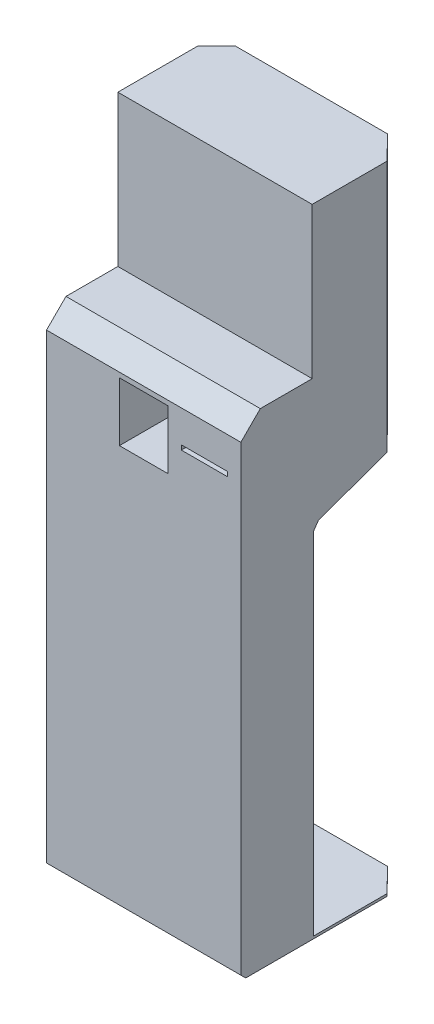
SolidWorks part; units mm, degrees
ref_plane "Front Plane" through (0, 0, 0) normal (0, 0, 1) x (1, 0, 0)
ref_plane "Top Plane" through (0, 0, 0) normal (0, 1, 0) x (1, 0, 0)
ref_plane "Right Plane" through (0, 0, 0) normal (1, 0, 0) x (0, 0, -1)
sketch "Sketch1" plane through (0, 0, 0) normal (1, 0, 0) x (0, 0, -1)
  line L0 (0, 0) -> (-340, 0)
  line L1 (-350, 10) -> (-350, 960)
  line L2 (-310, 1000) -> (-203.2511, 1000)
  line L3 (-203.2511, 1000) -> (-203.2511, 1310.6969)
  line L4 (0, 970) -> (0, 820)
  line L5 (-203.2511, 1310.6969) -> (-350, 1000) construction
  line L6 (-203.2511, 1310.6969) -> (-108.4889, 1310.6969)
  line L7 (-108.4889, 1310.6969) -> (-9.8898, 1028.323) construction
  line L8 (-310, 1000) -> (-350, 960)
  line L9 (-27.4748, 800) -> (-180, 800) construction
  line L10 (-200, 780) -> (-200, 20) construction
  line L11 (-190, 10) -> (0, 10) construction
  line L12 (0, 10) -> (0, 0) construction
  line L13 (-200, 20) -> (-190, 10) construction
  line L14 (-340, 0) -> (-350, 10)
  line L15 (-180, 800) -> (-200, 780) construction
  line L16 (-9.3969, 806.5798) -> (-27.4748, 800)
  line L17 (-27.4748, 800) -> (-190.6031, 740.6262)
  line L18 (-200, 727.206) -> (-200, 5)
  line L19 (0, 1000) -> (0, 1310.6969)
  line L20 (0, 1310.6969) -> (-108.4889, 1310.6969)
  line L21 (-9.8898, 1028.323) -> (0, 970) construction
  line L22 (0, 820) -> (-9.3969, 806.5798)
  line L23 (-190.6031, 740.6262) -> (-200, 727.206)
  line L24 (0, 1000) -> (0, 970)
  line L25 (0, 10) -> (-200, 70) construction
  line L26 (-200, 5) -> (0, 5)
  line L27 (0, 5) -> (0, 0)
  arc A0 (0, 1000) -> (-203.2511, 1310.6969) centre (-339.0968, 1000) ccw construction
  arc A1 (-350, 960) -> (-310, 1000) centre (-310, 960) cw construction
  point P1 (-350, 0)
  point P12 (0, 800)
  point P13 (-200, 800)
  point P15 (-200, 10)
  point P23 (0, 810)
  point P25 (-200, 737.206)
  dimension "D5" = 40
  dimension "D1" = 1000
  dimension "D2" = 350
  dimension "D3" = 310.6969
  dimension "D7" = 150
  dimension "D8" = 10
  dimension "D10" = 110
  dimension "D9" = 200
  dimension "D15" = 60
  dimension "D16" = 5
extrude "Boss-Extrude1" add sketch "Sketch1" along normal blind 400
sketch "Sketch2" plane through (0, 0, 350) normal (0, 0, 1) x (1, 0, 0)
  line L0 (200, 950) -> (200, 1000) construction
  line L1 (150, 950) -> (250, 950)
  line L2 (150, 950) -> (150, 829)
  line L3 (150, 829) -> (250, 829)
  line L4 (250, 950) -> (250, 829)
  line L5 (400, 1000) -> (0, 1000) construction
  line L6 (277.35, 889.5) -> (250, 889.5) construction
  line L7 (372.65, 894.2) -> (277.35, 894.2)
  line L8 (372.65, 894.2) -> (372.65, 884.8)
  line L9 (372.65, 884.8) -> (277.35, 884.8)
  line L10 (277.35, 894.2) -> (277.35, 884.8)
  line L11 (250, 950) -> (400, 950) construction
  line L12 (400, 960) -> (400, 10) construction
  line L13 (325, 950) -> (325, 894.2) construction
  dimension "D1" = 121
  dimension "D2" = 100
  dimension "D3" = 50
  dimension "D4" = 9.4
  dimension "D5" = 95.3
extrude "Cut-Extrude1" cut sketch "Sketch2" against normal blind 268
sketch "Sketch3" plane through (0, 0, 0) normal (0, -1, 0) x (-1, 0, 0)
  line L0 (32.9719, -72.8044) -> (-67.7282, 29.5696)
  line L1 (-67.7282, 29.5696) -> (-322.6486, 29.5696)
  line L2 (-322.6486, 29.5696) -> (-423.3487, -72.8044)
  line L3 (-423.3487, -72.8044) -> (-423.3487, 100.0695)
  line L4 (-423.3487, 100.0695) -> (32.9719, 100.0695)
  line L5 (32.9719, 100.0695) -> (32.9719, -72.8044)
  line L6 (-195.1884, 29.5696) -> (-195.1884, -2.4875) construction
  line L8 (-195.1884, 29.5696) -> (-195.1884, 100.0695) construction
extrude "Cut-Extrude2" cut sketch "Sketch3" against normal through all both and the other way through all
